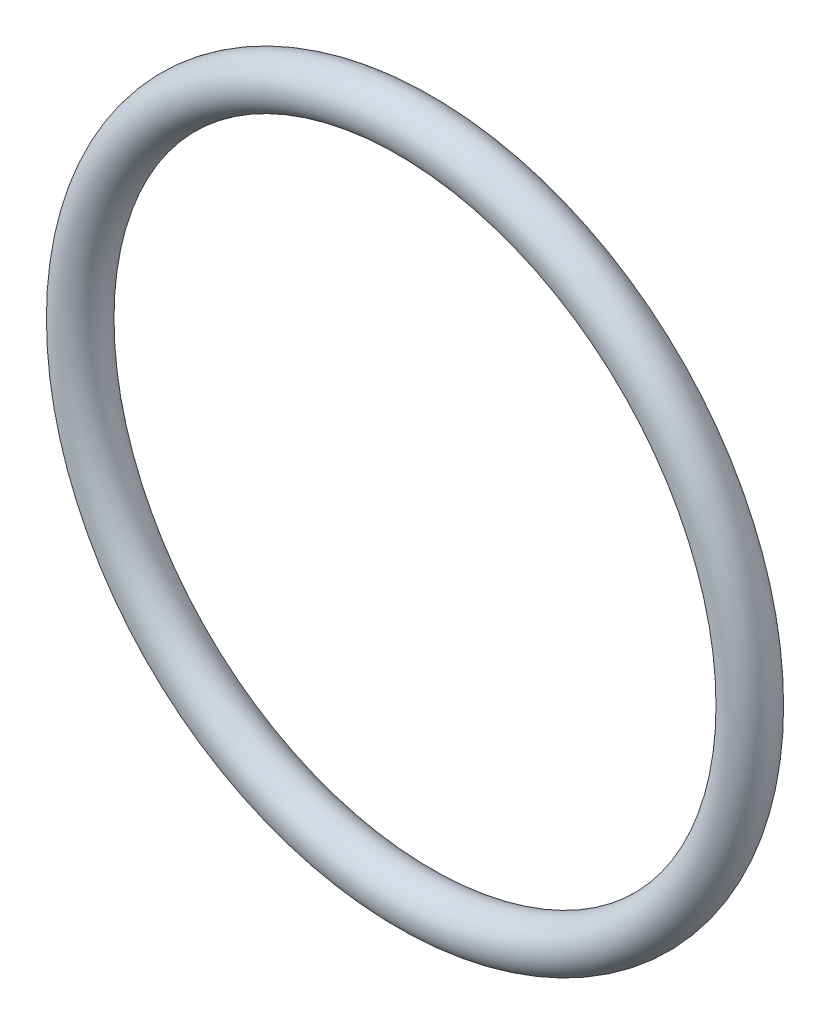
SolidWorks part; units mm, degrees
ref_plane "Front" through (0, 0, 0) normal (0, 0, 1) x (1, 0, 0)
ref_plane "Top" through (0, 0, 0) normal (0, 1, 0) x (1, 0, 0)
ref_plane "Right" through (0, 0, 0) normal (1, 0, 0) x (0, 0, -1)
sketch "Sketch1" plane through (0, 0, 0) normal (0, 0, 1) x (1, 0, 0)
  circle A0 centre (0, 0) radius 6.5 construction
  circle A1 centre (0, 0) radius 7.5 construction
  point P4 (6.5, 0)
  point P5 (7.5, 0)
  dimension "ID" = 13
  dimension "OD" = 15
sketch "Sketch2" plane through (0, 0, 0) normal (1, 0, 0) x (0, 0, -1)
  line L0 (-0.5, 0) -> (0.5, 0) construction
  dimension "Width" = 1
sketch "Sketch3" plane through (0, 0, 0) normal (0, 1, 0) x (1, 0, 0)
  line L2 (0, -0.5) -> (0, 0.5) construction
  line L7 (7, -0.5) -> (7, 0.5) construction
  circle A0 centre (7, 0) radius 0.5
revolve "Revolve1" add sketch "Sketch3" angle 360 about L0
